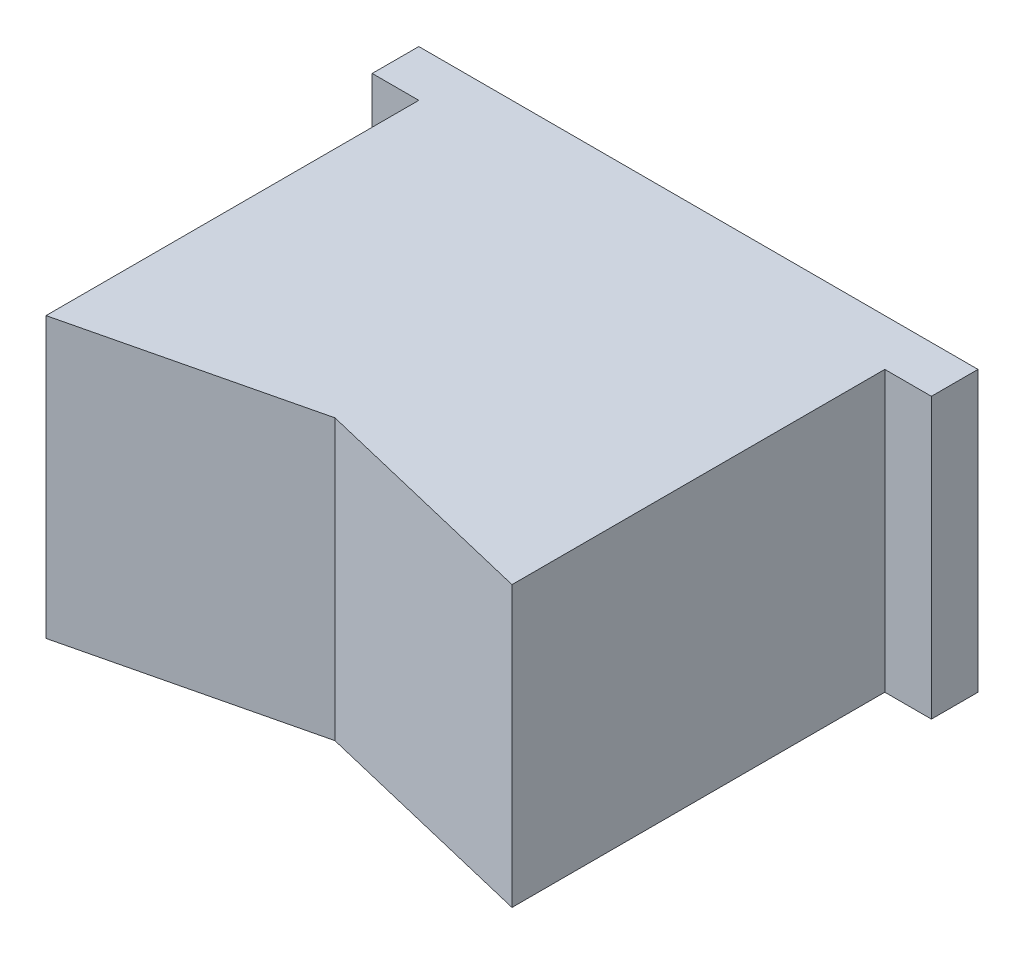
SolidWorks part; units mm, degrees
ref_plane "Alzado" through (0, 0, 0) normal (0, 0, 1) x (1, 0, 0)
ref_plane "Planta" through (0, 0, 0) normal (0, 1, 0) x (1, 0, 0)
ref_plane "Vista lateral" through (0, 0, 0) normal (1, 0, 0) x (0, 0, -1)
sketch "Croquis1" plane through (0, 0, 0) normal (0, 0, 1) x (1, 0, 0)
  line L1 (-15, 7.5) -> (15, 7.5)
  line L2 (-15, 7.5) -> (-15, -7.5)
  line L3 (-15, -7.5) -> (15, -7.5)
  line L4 (15, 7.5) -> (15, -7.5)
  line L5 (-15, 7.5) -> (15, -7.5) construction
  line L6 (-15, -7.5) -> (15, 7.5) construction
  point P0 (0, 0)
  dimension "D1" = 15
  dimension "D2" = 30
extrude "Saliente-Extruir1" add sketch "Croquis1" along normal blind 2.5
sketch "Croquis2" plane through (0, 0, 2.5) normal (0, 0, 1) x (1, 0, 0)
  line L1 (-12.5, 7.5) -> (12.5, 7.5)
  line L2 (-12.5, 7.5) -> (-12.5, -7.5)
  line L3 (-12.5, -7.5) -> (12.5, -7.5)
  line L4 (12.5, 7.5) -> (12.5, -7.5)
  line L5 (-12.5, 7.5) -> (12.5, -7.5) construction
  line L6 (-12.5, -7.5) -> (12.5, 7.5) construction
  point P0 (0, 0)
  dimension "D1" = 25
  dimension "D2" = 15
extrude "Saliente-Extruir2" add sketch "Croquis2" along normal blind 20
sketch "Croquis4" plane through (0, 7.5, 0) normal (0, 1, 0) x (1, 0, 0)
  line L0 (-12.5, -22.5) -> (0, -19.5)
  line L1 (0, -19.5) -> (12.5, -22.5)
  line L3 (12.5, -22.5) -> (-12.5, -22.5) construction
  line L4 (-12.5, -22.5) -> (12.5, -22.5)
  point P7 (0, -22.5)
  dimension "D1" = 3
extrude "Cortar-Extruir1" cut sketch "Croquis4" against normal blind 20
sketch "Croquis5" plane through (0, 0, 0) normal (0, 0, -1) x (-1, 0, 0)
  line L0 (15, -7.5) -> (-15, -7.5) construction
  circle A0 centre (-7, 0) radius 5
  circle A1 centre (7, 0) radius 5
  point P7 (0, -7.5)
  dimension "D1" = 10
  dimension "D2" = 7.5
  dimension "D3" = 7.5
  dimension "D4" = 7
  dimension "D5" = 7
extrude "Cortar-Extruir3" cut sketch "Croquis5" against normal blind 4.6
